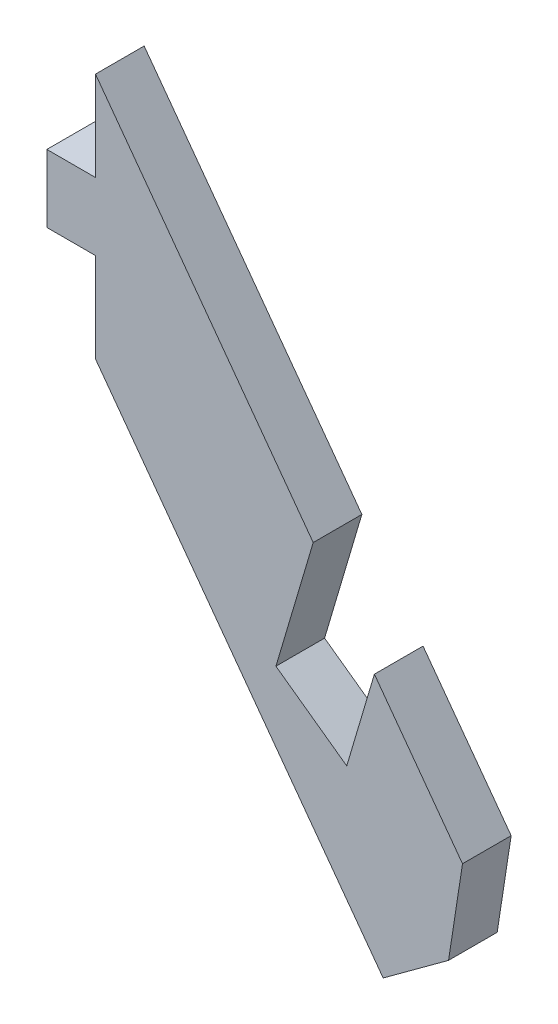
SolidWorks part; units mm, degrees
ref_plane "Front Plane" through (0, 0, 0) normal (0, 0, 1) x (1, 0, 0)
ref_plane "Top Plane" through (0, 0, 0) normal (0, 1, 0) x (1, 0, 0)
ref_plane "Right Plane" through (0, 0, 0) normal (1, 0, 0) x (0, 0, -1)
sketch "Sketch1" plane through (0, 0, 0) normal (0, 0, 1) x (1, 0, 0)
  line L0 (0, 14.5) -> (0, -0.7175)
  line L1 (0, 14.5) -> (25, -19.5854)
  line L2 (25, -19.5854) -> (17.7428, -24.9083)
  line L3 (17.7428, -24.9083) -> (0, -0.7175)
  line L4 (0, 10) -> (4.8343, 10) construction
  dimension "D1" = 4.5
  dimension "D2" = 9
  dimension "D3" = 30
  dimension "D4" = 25
extrude "Boss-Extrude1" add sketch "Sketch1" against normal blind 3
sketch "Sketch2" plane through (0, 0, 0) normal (0, 0, 1) x (1, 0, 0)
  line L0 (0, 8.9763) -> (-3, 8.9763)
  line L1 (0, 14.5) -> (0, -0.7175) construction
  line L2 (-3, 16) -> (-3, 10) construction
  line L3 (-3, 8.9763) -> (-3, 4.8063)
  line L4 (-3, 10) -> (-3, 0) construction
  line L5 (-3, 4.8063) -> (0, 4.8063)
  line L7 (0, 6.8913) -> (-2.4254, 6.8913) construction
  line L10 (25, -19.5854) -> (0, 14.5)
  line L11 (0, 14.5) -> (0, -0.7175)
  line L12 (0, -0.7175) -> (17.7428, -24.9083)
  line L13 (17.7428, -24.9083) -> (25, -19.5854)
  line L15 (0, 8.9763) -> (0, 4.8063)
  dimension "D2" = 4.17
  dimension "D3" = 0
extrude "Boss-Extrude2" add sketch "Sketch2" against normal up to surface (3 mm away) up to face at (10.6857, -7.6778, -3)
sketch "Sketch3" plane through (0, 0, -3) normal (0, 0, -1) x (-1, 0, 0)
  line L0 (-17.7428, -24.9083) -> (-25, -19.5854) construction
  line L1 (0, 4.8063) -> (0, -0.7175) construction
  line L2 (-25, -19.5854) -> (0, 14.5) construction
  line L8 (-13.4271, -3.8068) -> (-17.2006, -8.9515)
  line L9 (-17.2006, -8.9515) -> (-15.4953, -14.7041)
  line L10 (-15.4953, -14.7041) -> (-11.1279, -11.5634)
  line L11 (-11.1279, -11.5634) -> (-13.4271, -3.8068)
  dimension "D1" = 5.08
  dimension "D2" = 8.0902
  dimension "D3" = 5.7526
  dimension "D4" = 9.5574
  dimension "D5" = 16.511
extrude "Cut-Extrude2" cut sketch "Sketch3" against normal up to surface (3 mm away) up to face at (4.5928, -0.3933, 0)
chamfer "Chamfer1" distance 4 angle 45 1 edges at (25, -19.5854, -1.5)
